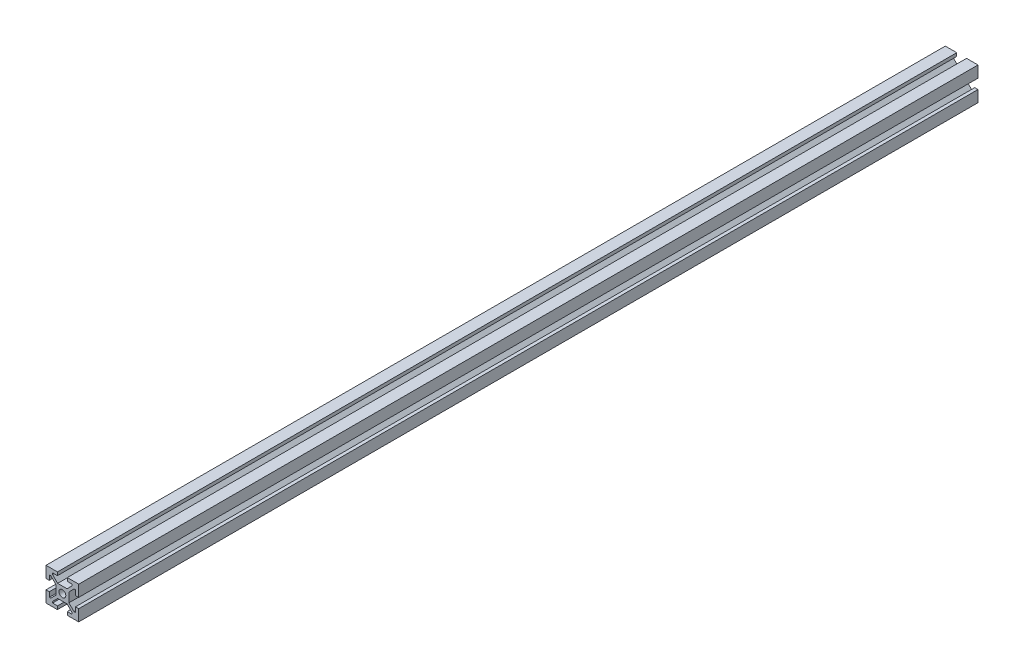
SolidWorks part; units mm, degrees
ref_plane "Alzado" through (0, 0, 0) normal (0, 0, 1) x (1, 0, 0)
ref_plane "Planta" through (0, 0, 0) normal (0, 1, 0) x (1, 0, 0)
ref_plane "Vista lateral" through (0, 0, 0) normal (1, 0, 0) x (0, 0, -1)
ref_plane "Plano1" through (0, 0, 420) normal (0, 0, 1) x (1, 0, 0)
sketch "Croquis1" plane through (0, 0, 420) normal (0, 0, 1) x (1, 0, 0)
  line L0 (-10, 10) -> (-10, 3)
  line L1 (-10, 3) -> (-8, 3)
  line L2 (-8, 3) -> (-8, 6)
  line L3 (-8, 6) -> (-7.1314, 6)
  line L4 (-7.1314, 6) -> (-4, 2.8686)
  line L5 (-4, 2.8686) -> (-4, -2.8686)
  line L6 (-4, -2.8686) -> (-7.1314, -6)
  line L7 (-7.1314, -6) -> (-8, -6)
  line L8 (-8, -6) -> (-8, -3)
  line L9 (-8, -3) -> (-10, -3)
  line L10 (-10, -3) -> (-10, -10)
  line L11 (-10, -10) -> (-3, -10)
  line L12 (-3, -10) -> (-3, -8)
  line L13 (-3, -8) -> (-6, -8)
  line L14 (-6, -8) -> (-6, -7.1314)
  line L15 (-6, -7.1314) -> (-2.8686, -4)
  line L16 (-2.8686, -4) -> (2.8686, -4)
  line L17 (2.8686, -4) -> (6, -7.1314)
  line L18 (6, -7.1314) -> (6, -8)
  line L19 (6, -8) -> (3, -8)
  line L20 (3, -8) -> (3, -10)
  line L21 (3, -10) -> (10, -10)
  line L22 (10, -10) -> (10, -3)
  line L23 (10, -3) -> (8, -3)
  line L24 (8, -3) -> (8, -6)
  line L25 (8, -6) -> (7.1314, -6)
  line L26 (7.1314, -6) -> (4, -2.8686)
  line L27 (4, -2.8686) -> (4, 2.8686)
  line L28 (4, 2.8686) -> (7.1314, 6)
  line L29 (7.1314, 6) -> (8, 6)
  line L30 (8, 6) -> (8, 3)
  line L31 (8, 3) -> (10, 3)
  line L32 (10, 3) -> (10, 10)
  line L33 (10, 10) -> (3, 10)
  line L34 (3, 10) -> (3, 8)
  line L35 (3, 8) -> (6, 8)
  line L36 (6, 8) -> (6, 7.1314)
  line L37 (6, 7.1314) -> (2.8686, 4)
  line L38 (2.8686, 4) -> (-2.8686, 4)
  line L39 (-2.8686, 4) -> (-6, 7.1314)
  line L40 (-6, 7.1314) -> (-6, 8)
  line L41 (-6, 8) -> (-3, 8)
  line L42 (-3, 8) -> (-3, 10)
  line L43 (-3, 10) -> (-10, 10)
  circle A0 centre (0, 0) radius 2.1
extrude "Saliente-Extruir1" add sketch "Croquis1" against normal blind 550
